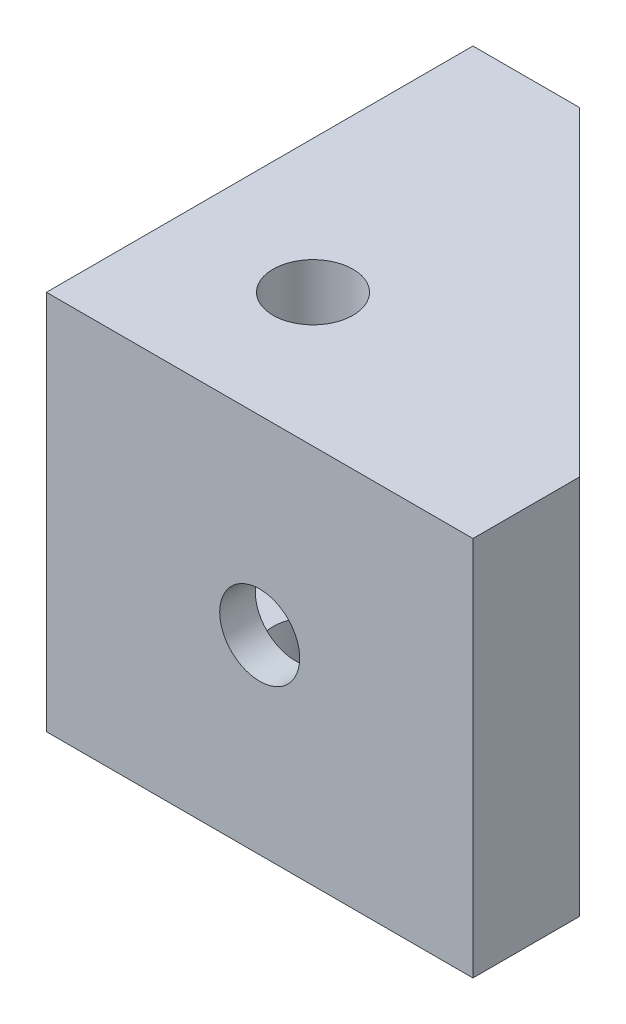
SolidWorks part; units mm, degrees
ref_plane "Front Plane" through (0, 0, 0) normal (0, 0, 1) x (1, 0, 0)
ref_plane "Top Plane" through (0, 0, 0) normal (0, 1, 0) x (1, 0, 0)
ref_plane "Right Plane" through (0, 0, 0) normal (1, 0, 0) x (0, 0, -1)
sketch "Sketch1" plane through (0, 0, 0) normal (0, 1, 0) x (1, 0, 0)
  line L1 (0, 0) -> (38.1, 0)
  line L5 (0, 0) -> (0, 38.1)
  line L6 (0, 38.1) -> (9.525, 38.1)
  line L7 (9.525, 38.1) -> (38.1, 9.525)
  line L8 (38.1, 9.525) -> (38.1, 0)
  dimension "D1" = 38.1
  dimension "D2" = 9.525
extrude "Main Body" add sketch "Sketch1" along normal blind 34
sketch "Sketch3" plane through (0, 0, 0) normal (0, 0, 1) x (1, 0, 0)
  line L0 (0, 0) -> (38.1, 34) construction
  circle A0 centre (19.05, 17) radius 3.5719
  circle A1 centre (19.05, 17) radius 7.9375 construction
  dimension "D1" = 7.1437
  dimension "D2" = 15.875
extrude "9/32 Right Rail" cut sketch "Sketch3" against normal through all both and the other way through all
sketch "Sketch4" plane through (0, 0, 0) normal (-1, 0, 0) x (0, 0, 1)
  line L0 (0, 0) -> (-38.1, 34) construction
  circle A0 centre (-19.05, 17) radius 3.5719
  circle A1 centre (-19.05, 17) radius 7.9375 construction
  dimension "D1" = 7.1437
  dimension "D2" = 15.875
extrude "9/32 Left Rail" cut sketch "Sketch4" against normal blind 34
ref_plane "Plane1" through (0, 27.65, 0) normal (0, 1, 0) x (1, 0, 0)
sketch "Sketch5" plane through (0, 27.65, 0) normal (0, 1, 0) x (1, 0, 0)
  line L1 (23.8125, 23.8125) -> (0, 0) construction
  line L2 (0, 38.1) -> (0, 0) construction
  line L5 (3.175, 28.3824) -> (11.2088, 36.4162)
  line L6 (38.1, 9.525) -> (9.525, 38.1) construction
  line L7 (11.2088, 36.4162) -> (36.4162, 11.2088)
  line L8 (36.4162, 11.2088) -> (28.3824, 3.175)
  line L9 (15.4781, 0) -> (22.6219, 0) construction
  line L15 (3.175, 28.3824) -> (3.175, 3.175)
  line L16 (3.175, 3.175) -> (28.3824, 3.175)
  line L20 (0, 22.6219) -> (0, 15.4781) construction
  line L21 (15.4781, 0) -> (22.6219, 0) construction
  line L22 (0, 22.6219) -> (0, 15.4781) construction
  point P13 (0, 0)
  point P16 (3.6248, 6.4845)
  point P17 (2.9171, 2.9171)
  point P21 (7.6651, 31.75)
  point P22 (4.8977, 28.9826)
  point P23 (3.175, 26.491)
  point P24 (4.1842, 28.269)
  point P25 (0, 0)
  point P26 (0, 0)
  dimension "D1" = 3.175
  dimension "D3" = 2.3812
extrude "Inner Hollow" cut sketch "Sketch5" against normal offset from surface (21.3 mm away) 6.35 up to face at (17.145, 0, -17.145)
sketch "Sketch6" plane through (0, 34, 0) normal (0, 1, 0) x (1, 0, 0)
  line L0 (23.8125, 23.8125) -> (0, 0) construction
  line L2 (38.1, 9.525) -> (9.525, 38.1) construction
  line L8 (36.4162, 11.2088) -> (11.2088, 36.4162)
  line L9 (28.3824, 3.175) -> (36.4162, 11.2088)
  line L10 (3.175, 3.175) -> (28.3824, 3.175)
  line L11 (3.175, 28.3824) -> (3.175, 3.175)
  line L12 (11.2088, 36.4162) -> (3.175, 28.3824)
  line L13 (36.4162, 11.2088) -> (11.2088, 36.4162) construction
  line L14 (28.3824, 3.175) -> (36.4162, 11.2088) construction
  line L15 (3.175, 3.175) -> (28.3824, 3.175) construction
  line L16 (3.175, 28.3824) -> (3.175, 3.175) construction
  line L17 (11.2088, 36.4162) -> (3.175, 28.3824) construction
  circle A1 centre (11.9063, 11.9063) radius 3.5719
  circle A2 centre (11.9063, 11.9063) radius 7.9375 construction
  point P12 (-9.8555, 13.3796)
  point P18 (-8.7817, 12.9368)
  point P19 (11.9063, 12.1542)
  dimension "D1" = 7.1437
  dimension "D3" = 15.875
  dimension "D2" = 0
extrude "9/32 Top Hole" cut sketch "Sketch6" against normal through all both and the other way through all
